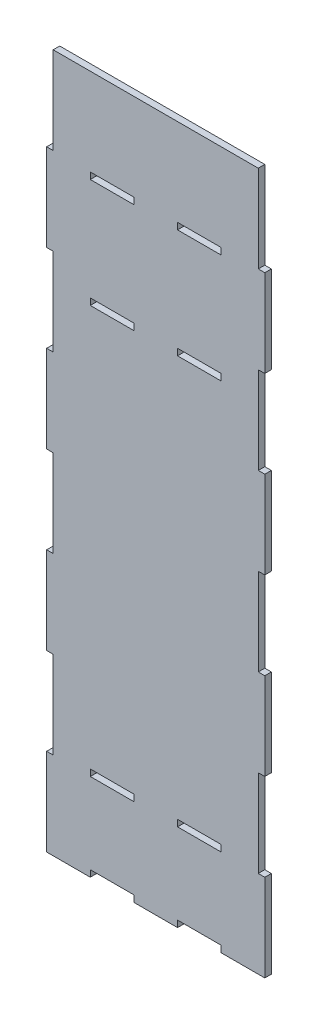
SolidWorks part; units mm, degrees
material "玻璃"
ref_plane "前视基准面" through (0, 0, 0) normal (0, 0, 1) x (1, 0, 0)
ref_plane "上视基准面" through (0, 0, 0) normal (0, 1, 0) x (1, 0, 0)
ref_plane "右视基准面" through (0, 0, 0) normal (1, 0, 0) x (0, 0, -1)
sketch "草图1" plane through (0, 0, 0) normal (0, 0, 1) x (1, 0, 0)
  line L0 (-30, -13.7162) -> (-10, -13.7162)
  line L1 (0, 306.377) -> (0, -104.9007) construction
  line L7 (50, -53.7162) -> (50, -13.7162)
  line L8 (50, -13.7162) -> (47, -13.7162)
  line L9 (47, -13.7162) -> (47, 26.2838)
  line L10 (47, 26.2838) -> (50, 26.2838)
  line L11 (50, 26.2838) -> (50, 66.2838)
  line L12 (50, 66.2838) -> (47, 66.2838)
  line L13 (47, 66.2838) -> (47, 106.2838)
  line L14 (47, 106.2838) -> (50, 106.2838)
  line L15 (50, 106.2838) -> (50, 146.2838)
  line L16 (50, 146.2838) -> (47, 146.2838)
  line L17 (47, 146.2838) -> (47, 186.2838)
  line L18 (47, 186.2838) -> (50, 186.2838)
  line L19 (50, 186.2838) -> (50, 226.2838)
  line L20 (50, 226.2838) -> (47, 226.2838)
  line L21 (47, 226.2838) -> (47, 266.2838)
  line L27 (148.3444, 0) -> (-124.5033, 0) construction
  line L32 (-47, 226.2838) -> (-47, 266.2838)
  line L33 (-50, 226.2838) -> (-47, 226.2838)
  line L34 (-50, 186.2838) -> (-50, 226.2838)
  line L35 (-47, 186.2838) -> (-50, 186.2838)
  line L36 (-47, 146.2838) -> (-47, 186.2838)
  line L37 (-50, 146.2838) -> (-47, 146.2838)
  line L38 (-50, 106.2838) -> (-50, 146.2838)
  line L39 (-47, 106.2838) -> (-50, 106.2838)
  line L40 (-47, 66.2838) -> (-47, 106.2838)
  line L41 (-50, 66.2838) -> (-47, 66.2838)
  line L42 (-50, 26.2838) -> (-50, 66.2838)
  line L43 (-47, 26.2838) -> (-50, 26.2838)
  line L44 (-47, -13.7162) -> (-47, 26.2838)
  line L45 (-50, -13.7162) -> (-47, -13.7162)
  line L46 (-50, -53.7162) -> (-50, -13.7162)
  line L63 (-50, -53.7162) -> (-30, -53.7162)
  line L64 (-30, -53.7162) -> (-30, -50.7162)
  line L65 (-30, -50.7162) -> (-10, -50.7162)
  line L66 (-10, -50.7162) -> (-10, -53.7162)
  line L67 (-10, -53.7162) -> (10, -53.7162)
  line L68 (10, -53.7162) -> (10, -50.7162)
  line L69 (10, -50.7162) -> (30, -50.7162)
  line L70 (30, -50.7162) -> (30, -53.7162)
  line L71 (30, -53.7162) -> (50, -53.7162)
  line L80 (-47, 266.2838) -> (47, 266.2838)
  line L81 (-10, -13.7162) -> (-10, -10.7162)
  line L82 (-10, -10.7162) -> (-30, -10.7162)
  line L83 (-30, -10.7162) -> (-30, -13.7162)
  line L84 (10, -13.7162) -> (10, -10.7162)
  line L85 (30, -10.7162) -> (30, -13.7162)
  line L86 (30, -13.7162) -> (10, -13.7162)
  line L87 (10, -10.7162) -> (30, -10.7162)
  line L88 (-30, 176.2838) -> (-30, 173.2838)
  line L89 (-30, 173.2838) -> (-10, 173.2838)
  line L90 (-10, 173.2838) -> (-10, 176.2838)
  line L91 (-10, 176.2838) -> (-30, 176.2838)
  line L92 (10, 173.2838) -> (10, 176.2838)
  line L93 (30, 176.2838) -> (30, 173.2838)
  line L94 (30, 173.2838) -> (10, 173.2838)
  line L95 (10, 176.2838) -> (30, 176.2838)
  line L96 (-30, 226.2838) -> (-10, 226.2838)
  line L97 (-10, 226.2838) -> (-10, 223.2838)
  line L98 (-10, 223.2838) -> (-30, 223.2838)
  line L99 (-30, 223.2838) -> (-30, 226.2838)
  line L100 (10, 226.2838) -> (10, 223.2838)
  line L101 (30, 226.2838) -> (10, 226.2838)
  line L102 (10, 223.2838) -> (30, 223.2838)
  line L103 (30, 223.2838) -> (30, 226.2838)
  point P35 (0, 269.404)
  point P58 (0, -53.7162)
  dimension "D1" = 20
  dimension "D2" = 20
  dimension "D3" = 20
  dimension "D4" = 20
  dimension "D5" = 3
  dimension "D6" = 3
  dimension "D7" = 90
  dimension "D8" = 3
  dimension "D9" = 20
  dimension "D10" = 20
  dimension "D11" = 3
  dimension "D12" = 40
extrude "凸台-拉伸1" add sketch "草图1" along normal blind 3
